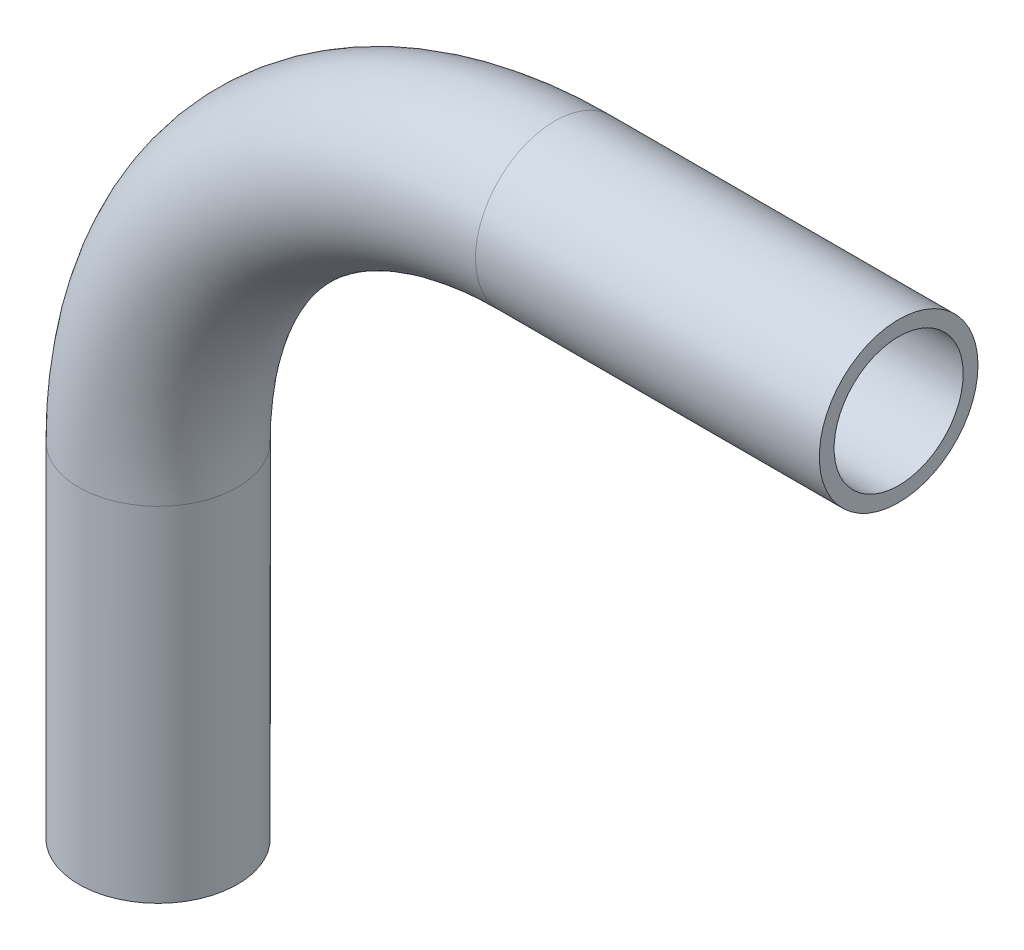
SolidWorks part; units mm, degrees
material "AISI 316 Stainless Steel Sheet (SS)"
ref_plane "Front Plane" through (0, 0, 0) normal (0, 0, 1) x (1, 0, 0)
ref_plane "Top Plane" through (0, 0, 0) normal (0, 1, 0) x (1, 0, 0)
ref_plane "Right Plane" through (0, 0, 0) normal (1, 0, 0) x (0, 0, -1)
sketch "Sketch1" plane through (0, 0, 0) normal (0, 0, 1) x (1, 0, 0)
  line L0 (0, -23.8125) -> (0, -44.45)
  line L1 (23.8125, 0) -> (44.45, 0)
  arc A0 (0, -23.8125) -> (23.8125, 0) centre (23.8125, -23.8125) cw
  point P6 (0, 0)
  dimension "D3" = 23.8125
  dimension "D1" = 44.45
  dimension "D2" = 44.45
ref_plane "Plane1" through (44.45, 0, 0) normal (1, 0, 0) x (0, 0, -1)
sketch "Sketch2" plane through (44.45, 0, 0) normal (1, 0, 0) x (0, 0, -1)
  circle A0 centre (0, 0) radius 4.7625
  circle A1 centre (0, 0) radius 3.8735
  dimension "D1" = 9.525
  dimension "D2" = 7.747
sweep "Sweep1" add profiles "Sketch2" path "Sketch1"
